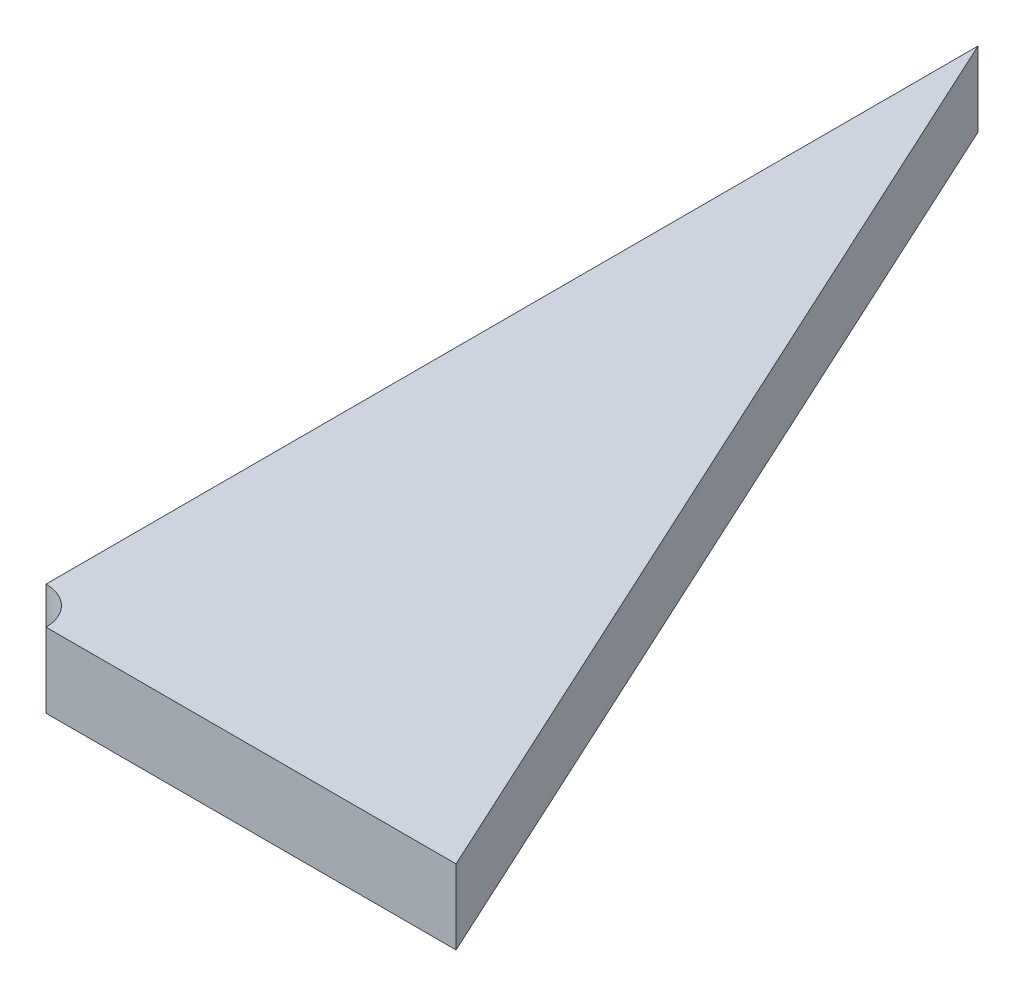
SolidWorks part; units mm, degrees
ref_plane "Front Plane" through (0, 0, 0) normal (0, 0, 1) x (1, 0, 0)
ref_plane "Top Plane" through (0, 0, 0) normal (0, 1, 0) x (1, 0, 0)
ref_plane "Right Plane" through (0, 0, 0) normal (1, 0, 0) x (0, 0, -1)
sketch "Sketch2" plane through (0, 0, 0) normal (0, 1, 0) x (1, 0, 0)
  line L0 (0, 0) -> (76.2, 0)
  line L1 (76.2, 0) -> (0, 165.1)
  line L2 (0, 165.1) -> (0, 0)
  dimension "D1" = 76.2
  dimension "D2" = 165.1
extrude "Boss-Extrude1" add sketch "Sketch2" along normal mid plane 12.7
sketch "Sketch3" plane through (0, 6.35, 0) normal (0, 1, 0) x (1, 0, 0)
  circle A0 centre (0, 0) radius 6.35
  dimension "D1" = 12.7
extrude "Cut-Extrude1" cut sketch "Sketch3" against normal up to next
